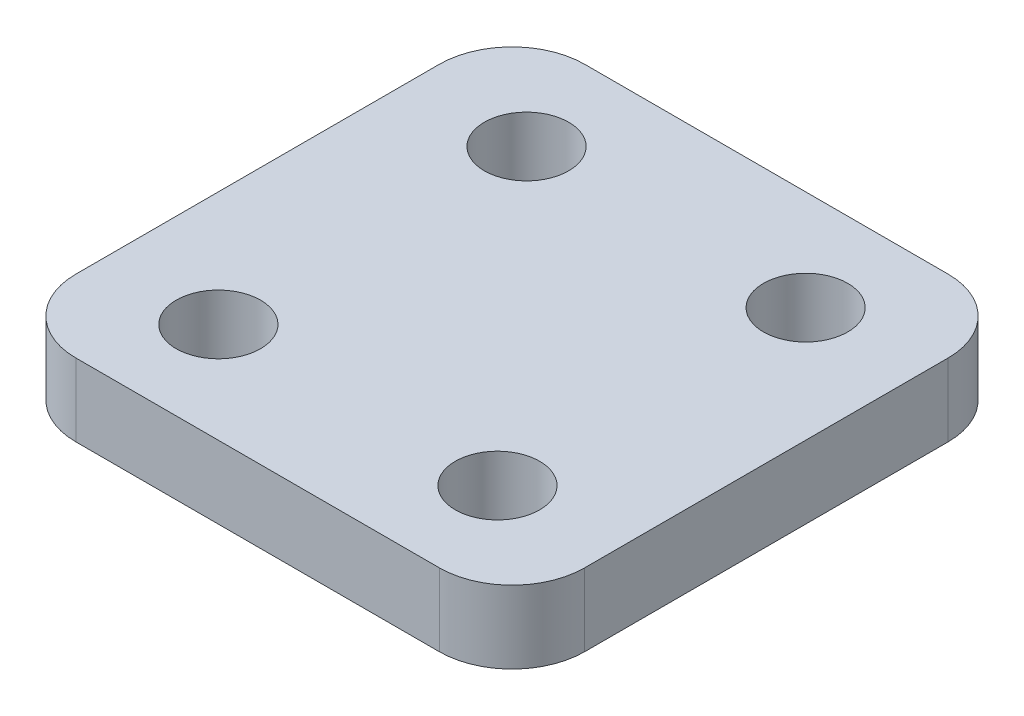
SolidWorks part; units mm, degrees
ref_plane "Front Plane" through (0, 0, 0) normal (0, 0, 1) x (1, 0, 0)
ref_plane "Top Plane" through (0, 0, 0) normal (0, 1, 0) x (1, 0, 0)
ref_plane "Right Plane" through (0, 0, 0) normal (1, 0, 0) x (0, 0, -1)
sketch "Sketch1" plane through (0, 0, 0) normal (0, 1, 0) x (1, 0, 0)
  line L1 (-8.89, -8.89) -> (8.89, -8.89)
  line L2 (-8.89, -8.89) -> (-8.89, 8.89)
  line L3 (-8.89, 8.89) -> (8.89, 8.89)
  line L4 (8.89, -8.89) -> (8.89, 8.89)
  line L5 (-8.89, -8.89) -> (8.89, 8.89) construction
  line L6 (-8.89, 8.89) -> (8.89, -8.89) construction
  point P0 (0, 0)
  dimension "D1" = 17.78
  dimension "D2" = 17.78
extrude "Boss-Extrude1" add sketch "Sketch1" along normal blind 2.54
sketch "Sketch2" plane through (0, 2.54, 0) normal (0, 1, 0) x (1, 0, 0)
  line L0 (8.89, 8.89) -> (-8.89, 8.89) construction
  line L1 (-8.89, 8.89) -> (-8.89, -8.89) construction
  line L2 (0, -8.89) -> (0, 8.89) construction
  line L3 (-8.89, -8.89) -> (8.89, -8.89) construction
  line L4 (-8.89, 0) -> (8.89, 0) construction
  line L5 (8.89, -8.89) -> (8.89, 8.89) construction
  circle A0 centre (-4.8768, 5.3848) radius 1.4732
  circle A1 centre (-4.8768, -5.3848) radius 1.4732
  circle A2 centre (4.8768, -5.3848) radius 1.4732
  circle A3 centre (4.8768, 5.3848) radius 1.4732
  point P2 (-6.35, 5.3848)
  point P3 (-4.8768, 6.858)
  dimension "D1" = 2.9464
  dimension "D2" = 2.032
  dimension "D3" = 2.54
extrude "Cut-Extrude1" cut sketch "Sketch2" against normal through all
fillet "Fillet1" radius 2.54 4 edges at (-8.89, 1.27, -8.89) (8.89, 1.27, -8.89) (8.89, 1.27, 8.89) (-8.89, 1.27, 8.89)
